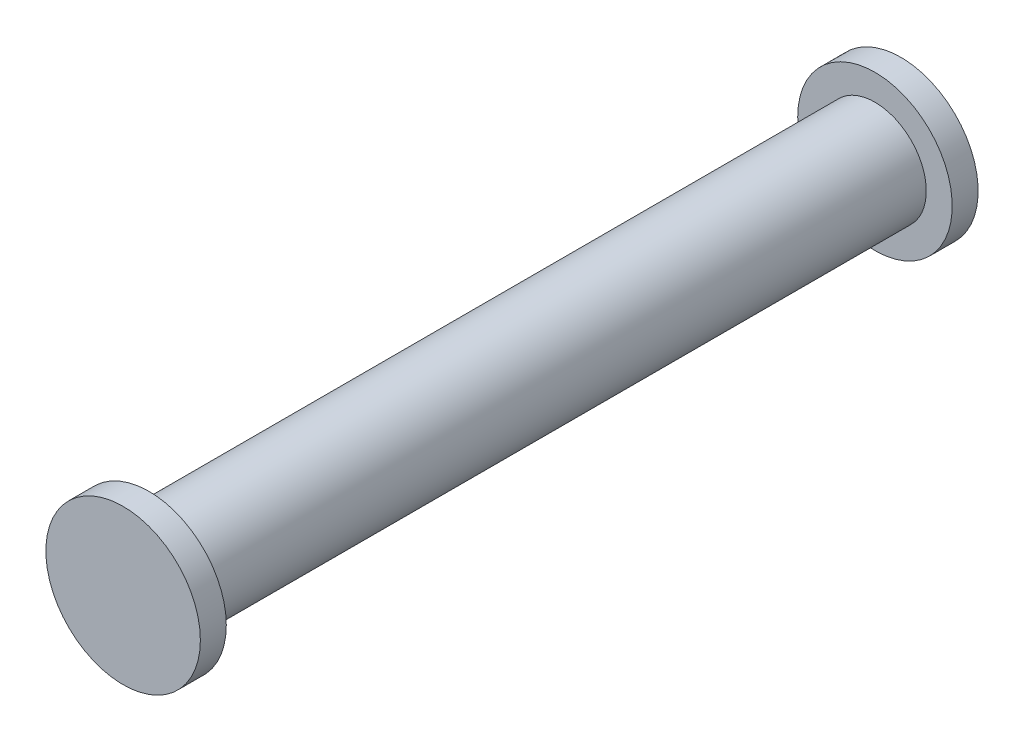
SolidWorks part; units mm, degrees
ref_plane "Front Plane" through (0, 0, 0) normal (0, 0, 1) x (1, 0, 0)
ref_plane "Top Plane" through (0, 0, 0) normal (0, 1, 0) x (1, 0, 0)
ref_plane "Right Plane" through (0, 0, 0) normal (1, 0, 0) x (0, 0, -1)
sketch "Sketch1" plane through (0, 0, 0) normal (0, 0, 1) x (1, 0, 0)
  circle A0 centre (0, 0) radius 4.95
  dimension "D1" = 9.9
extrude "Boss-Extrude1" add sketch "Sketch1" along normal blind 70
sketch "Sketch2" plane through (0, 0, 0) normal (0, 0, -1) x (-1, 0, 0)
  circle A2 centre (0, 0) radius 7.45
  circle A3 centre (0, 0) radius 7.45
  dimension "D1" = 2.5
extrude "Boss-Extrude2" add sketch "Sketch2" along normal blind 2.5
sketch "Sketch3" plane through (0, 0, 70) normal (0, 0, 1) x (1, 0, 0)
  circle A2 centre (0, 0) radius 7.45
  circle A3 centre (0, 0) radius 7.45
  dimension "D1" = 2.5
extrude "Boss-Extrude3" add sketch "Sketch3" along normal blind 2.5
